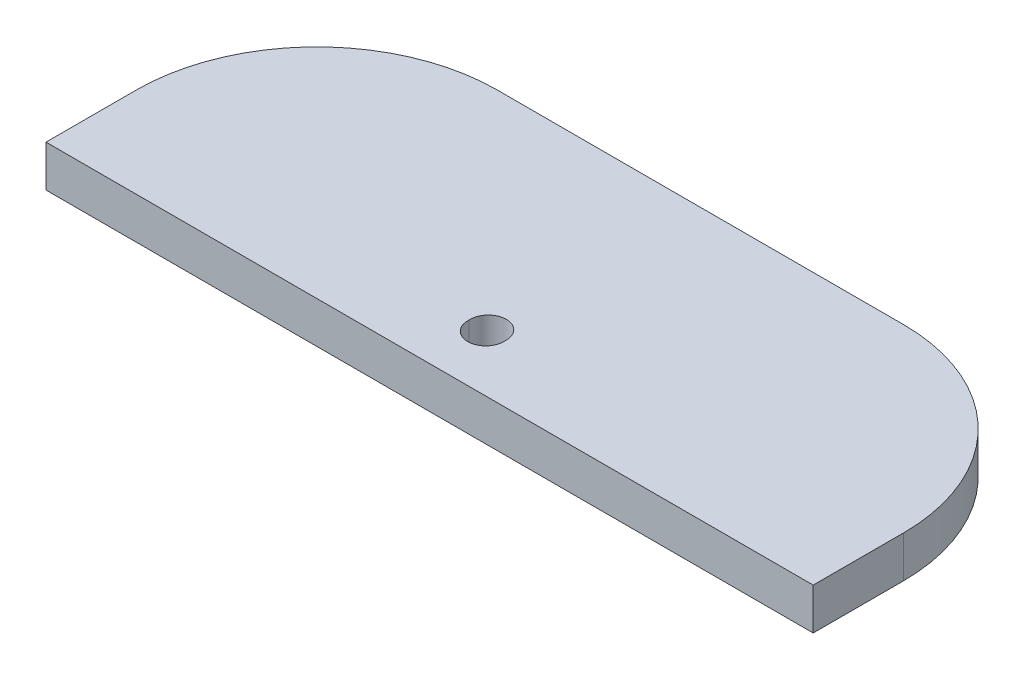
SolidWorks part; units mm, degrees
ref_plane "Front Plane" through (0, 0, 0) normal (0, 0, 1) x (1, 0, 0)
ref_plane "Top Plane" through (0, 0, 0) normal (0, 1, 0) x (1, 0, 0)
ref_plane "Right Plane" through (0, 0, 0) normal (1, 0, 0) x (0, 0, -1)
sketch "Sketch2" plane through (0, 0, 0) normal (0, 1, 0) x (1, 0, 0)
  line L1 (-21.25, 7.5) -> (21.25, 7.5)
  line L2 (-21.25, 7.5) -> (-21.25, -7.5)
  line L3 (-21.25, -7.5) -> (21.25, -7.5)
  line L4 (21.25, 7.5) -> (21.25, -7.5)
  line L5 (-21.25, 7.5) -> (21.25, -7.5) construction
  line L6 (-21.25, -7.5) -> (21.25, 7.5) construction
  circle A0 centre (0, -4.25) radius 1
  point P0 (0, 0)
  dimension "D3" = 2
  dimension "D1" = 42.5
  dimension "D2" = 15
extrude "Boss-Extrude1" add sketch "Sketch2" along normal blind 2.3
fillet "Fillet9" radius 10 2 edges at (21.25, 1.15, -7.5) (-21.25, 1.15, -7.5)
sketch "Sketch3" plane through (0, 2.3, 0) normal (0, 1, 0) x (1, 0, 0)
  circle A0 centre (0, -4.3887) radius 1
  dimension "D1" = 2
extrude "Cut-Extrude1" cut sketch "Sketch3" against normal through all
